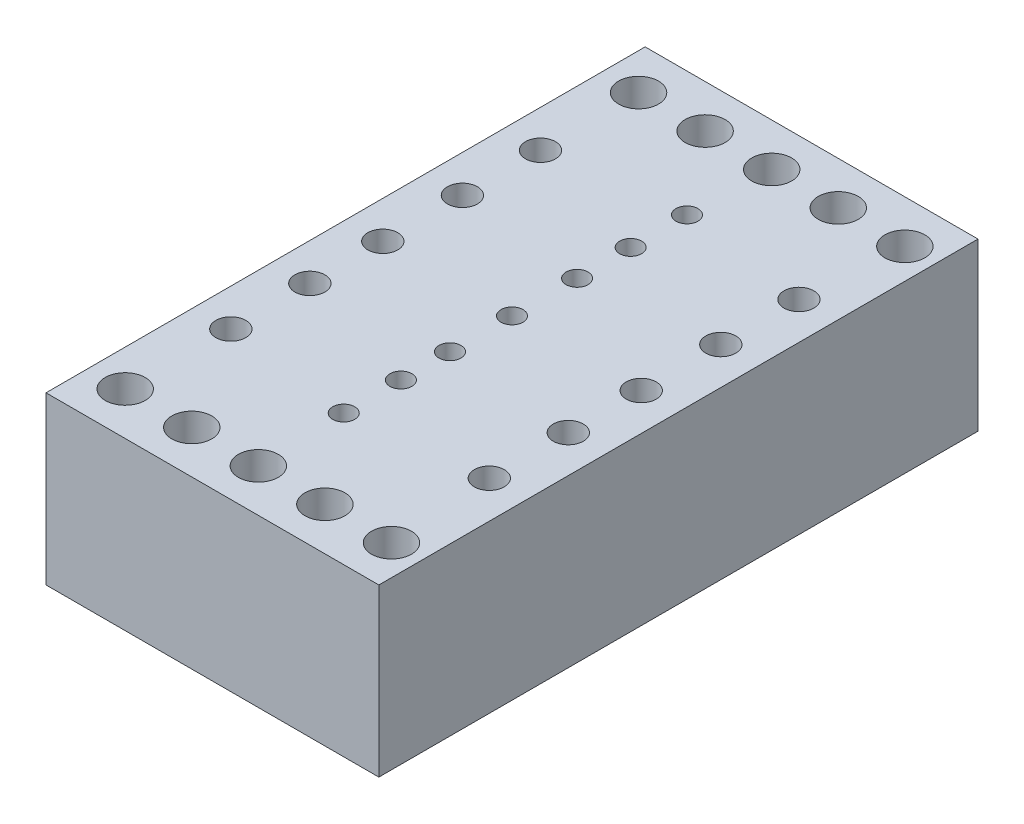
SolidWorks part; units mm, degrees
ref_plane "Alzado" through (0, 0, 0) normal (0, 0, 1) x (1, 0, 0)
ref_plane "Planta" through (0, 0, 0) normal (0, 1, 0) x (1, 0, 0)
ref_plane "Vista lateral" through (0, 0, 0) normal (1, 0, 0) x (0, 0, -1)
sketch "Croquis1" plane through (0, 0, 0) normal (0, 1, 0) x (1, 0, 0)
  line L1 (-50, 90) -> (50, 90)
  line L2 (-50, 90) -> (-50, -90)
  line L3 (-50, -90) -> (50, -90)
  line L4 (50, 90) -> (50, -90)
  line L5 (-50, 90) -> (50, -90) construction
  line L6 (-50, -90) -> (50, 90) construction
  point P0 (0, 0)
  dimension "D1" = 180
  dimension "D2" = 100
extrude "Saliente-Extruir1" add sketch "Croquis1" along normal blind 50
hole_wizard "Taladro1" positions "Croquis4" profile "Croquis3" legacy end condition through all
sketch "Croquis4" plane through (0, 50, 0) normal (0, 1, 0) x (1, 0, 0)
  point P0 (-39.0923, 77.1145)
sketch "Croquis3" plane through (-39.0923, 50, -77.1145) normal (1, 0, 0) x (0, 0, 1)
  line L0 (0, 0) -> (0, 50)
  line L1 (0, 50) -> (6, 50)
  line L2 (6, 50) -> (6, 0)
  line L3 (6, 0) -> (0, 0)
  line L4 (0, 110) -> (0, -10) construction
  dimension "Diámetro" = 12
  dimension "Profundidad" = 50
pattern_linear "MatrizL1" count 5 spacing 20 along (1, 0, 0) of "Taladro1"
mirror "Simetría1" about plane through (0, 0, 0) normal (0, 0, 1) of "MatrizL1", "Taladro1"
hole_wizard "Taladro de margen para M81" positions "Croquis5" profile "Croquis6" hole size "M8" standard "Ansi Metric"
sketch "Croquis5" plane through (0, 50, 0) normal (0, 1, 0) x (1, 0, 0)
  point P0 (-38.8195, 47.3796)
  point P2 (-38.8195, 0)
  point P4 (-38.8195, -45.6441)
  point P6 (-38.8195, 23.9191)
  point P8 (-38.8195, -21.9108)
sketch "Croquis6" plane through (-38.8195, 50, -47.3796) normal (1, 0, 0) x (0, 0, 1)
  line L0 (0, 0) -> (0, 28.1039)
  line L1 (0, 28.1039) -> (4.5, 25.4)
  line L2 (4.5, 25.4) -> (4.5, 0)
  line L5 (4.5, 0) -> (0, 0)
  line L10 (0, 28.1039) -> (-4.5, 25.4) construction
  line L11 (0, -6.35) -> (0, 107.95) construction
  dimension "Diámetro de taladro" = 9
  dimension "Profundidad de taladro" = 25.4
  dimension "Ángulo de perforador" = 118
mirror "Simetría2" about plane through (0, 0, 0) normal (1, 0, 0) of "Taladro de margen para M81"
hole_wizard "Taladro de margen para M61" positions "Croquis7" profile "Croquis8" hole size "M6" standard "Ansi Metric"
sketch "Croquis7" plane through (0, 50, 0) normal (0, 1, 0) x (1, 0, 0)
  point P0 (0, 52.5628)
  point P2 (0, 35.6494)
  point P4 (0, 19.5544)
  point P6 (0, 0)
  point P9 (0, -18.6372)
  point P11 (0, -33.3682)
  point P13 (0, -50.5544)
sketch "Croquis8" plane through (0, 50, -52.5628) normal (1, 0, 0) x (0, 0, 1)
  line L0 (0, 0) -> (0, 41.9828)
  line L1 (0, 41.9828) -> (3.3, 40)
  line L2 (3.3, 40) -> (3.3, 0)
  line L5 (3.3, 0) -> (0, 0)
  line L10 (0, 41.9828) -> (-3.3, 40) construction
  line L11 (0, -6.35) -> (0, 107.95) construction
  dimension "Diámetro de taladro" = 6.6
  dimension "Profundidad de taladro" = 40
  dimension "Ángulo de perforador" = 118
